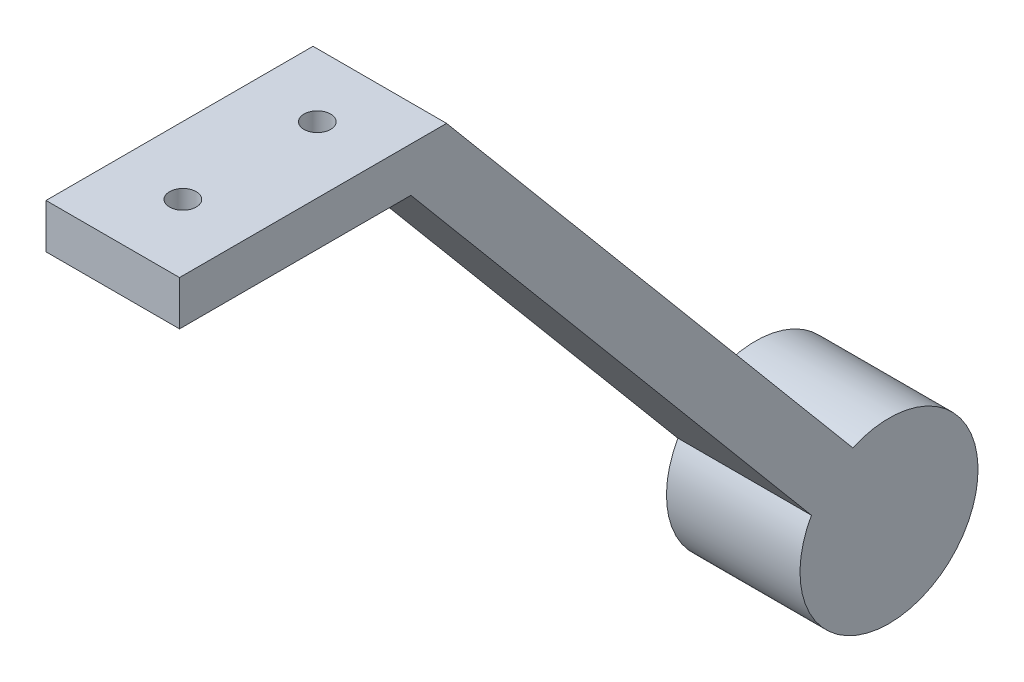
SolidWorks part; units mm, degrees
ref_plane "Front Plane" through (0, 0, 0) normal (0, 0, 1) x (1, 0, 0)
ref_plane "Top Plane" through (0, 0, 0) normal (0, 1, 0) x (1, 0, 0)
ref_plane "Right Plane" through (0, 0, 0) normal (1, 0, 0) x (0, 0, -1)
sketch "Sketch2" plane through (0, 0, 0) normal (1, 0, 0) x (0, 0, -1)
  line L0 (-22.8989, 5) -> (7.1011, 5)
  line L1 (7.1011, 5) -> (52.739, -49.3892)
  line L4 (3.0947, 0) -> (-22.8989, 0)
  line L5 (-22.8989, 0) -> (-22.8989, 5)
  line L6 (3.0947, 0) -> (48.0898, -53.6231)
  arc A1 (48.0898, -53.6231) -> (52.739, -49.3892) centre (56.8062, -58.5247) ccw
  point P8 (-1.5748, 0)
  dimension "D6" = 10
  dimension "D1" = 30
  dimension "D2" = 5
  dimension "D3" = 130
  dimension "D4" = 70
  dimension "D5" = 71
extrude "Boss-Extrude1" add sketch "Sketch2" against normal blind 15
sketch "Sketch3" plane through (0, 5, 0) normal (0, 1, 0) x (1, 0, 0)
  circle A0 centre (-7.4172, 0) radius 1.5
  circle A1 centre (-7.4172, -15.1038) radius 1.5
  dimension "D1" = 3
extrude "Cut-Extrude1" cut sketch "Sketch3" against normal blind 15
